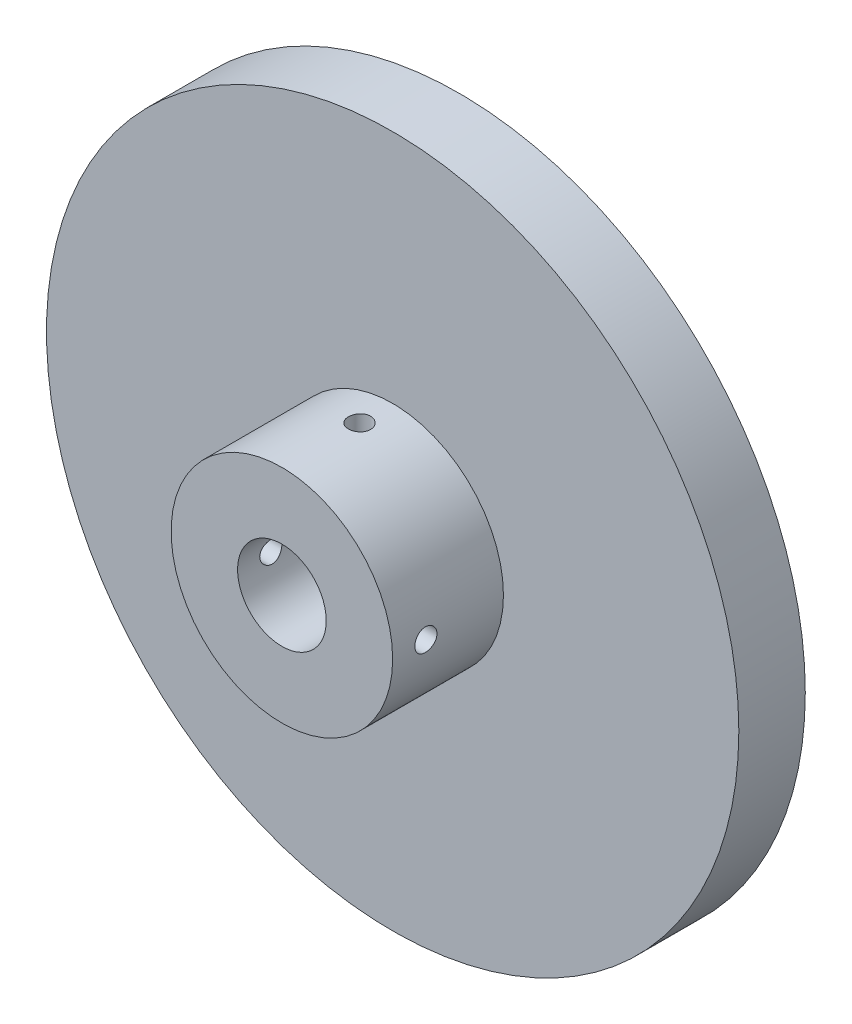
SolidWorks part; units mm, degrees
ref_plane "Front" through (0, 0, 0) normal (0, 0, 1) x (1, 0, 0)
ref_plane "Top" through (0, 0, 0) normal (0, 1, 0) x (1, 0, 0)
ref_plane "Right" through (0, 0, 0) normal (1, 0, 0) x (0, 0, -1)
sketch "Эскиз1" plane through (0, 0, 0) normal (0, 0, 1) x (1, 0, 0)
  circle A0 centre (0, 0) radius 31.25
  circle A1 centre (0, 0) radius 4
  dimension "D1" = 8
  dimension "D2" = 62.5
extrude "Бобышка-Вытянуть1" add sketch "Эскиз1" along normal blind 6
sketch "Эскиз2" plane through (0, 0, 6) normal (0, 0, 1) x (1, 0, 0)
  circle A0 centre (0, 0) radius 4 construction
  circle A1 centre (0, 0) radius 4
  circle A2 centre (0, 0) radius 10
  dimension "D1" = 20
extrude "Бобышка-Вытянуть2" add sketch "Эскиз2" along normal blind 10
sketch "Эскиз3" plane through (0, 0, 0) normal (0, 1, 0) x (1, 0, 0)
  line L0 (-10, -16) -> (10, -16) construction
  line L1 (-10, -16) -> (10, -16)
  line L2 (-10, -6) -> (10, -6) construction
  line L3 (-10, -6) -> (10, -6)
  line L4 (0, -16) -> (0, -6) construction
  circle A0 centre (0, -9) radius 1
  dimension "D1" = 2
  dimension "D2" = 3
extrude "Вырез-Вытянуть1" cut sketch "Эскиз3" against normal through all both and the other way through all contours L4 A0
sketch "Эскиз4" plane through (0, 0, 0) normal (1, 0, 0) x (0, 0, -1)
  line L0 (-16, 10) -> (-16, -10) construction
  line L1 (-16, 10) -> (-16, -10)
  line L2 (-6, 10) -> (-6, -10) construction
  line L3 (-6, 10) -> (-6, -10)
  line L4 (-16, 0) -> (-6, 0) construction
  circle A0 centre (-13, 0) radius 1
  dimension "D1" = 2
  dimension "D2" = 3
extrude "Вырез-Вытянуть2" cut sketch "Эскиз4" against normal through all both and the other way through all contours L4 A0 | A0 L4
